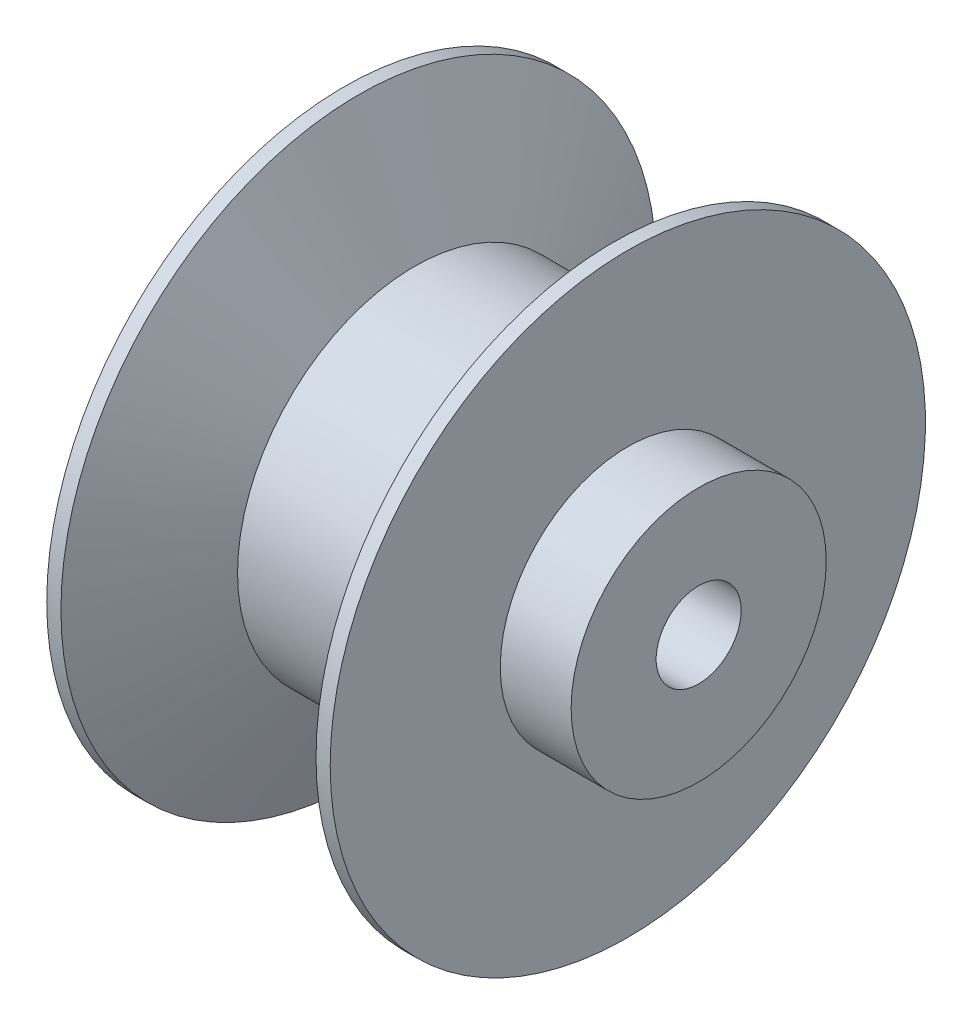
SolidWorks part; units mm, degrees
ref_plane "Plan de face" through (0, 0, 0) normal (0, 0, 1) x (1, 0, 0)
ref_plane "Plan de dessus" through (0, 0, 0) normal (0, 1, 0) x (1, 0, 0)
ref_plane "Plan de droite" through (0, 0, 0) normal (1, 0, 0) x (0, 0, -1)
sketch "Esquisse1" plane through (0, 0, 0) normal (0, 0, 1) x (1, 0, 0)
  line L0 (-128.7234, 0) -> (81.5011, 0) construction
  line L1 (-55.6577, 42) -> (-53.6577, 42)
  line L2 (-53.6577, 42) -> (-45.7304, 25)
  line L3 (-45.7304, 25) -> (-25.5849, 25)
  line L4 (-55.6577, 42) -> (-55.6577, 18)
  line L5 (-65.6577, 3) -> (-5.6577, 3)
  line L6 (-55.6577, 18) -> (-65.6577, 18)
  line L7 (-65.6577, 18) -> (-65.6577, 3)
  line L9 (-5.6577, 18) -> (-5.6577, 3)
  line L10 (-15.6577, 18) -> (-5.6577, 18)
  line L11 (-15.6577, 42) -> (-15.6577, 18)
  line L12 (-17.6577, 42) -> (-25.5849, 25)
  line L13 (-15.6577, 42) -> (-17.6577, 42)
  point P7 (-35.6577, 25)
  point P16 (-35.6577, 3)
  point P18 (-35.6577, 25)
  point P19 (-35.6577, 3)
  point P21 (-35.6577, 25)
  dimension "D1" = 0
  dimension "D2" = 25
  dimension "D3" = 42
  dimension "D4" = 0
  dimension "D5" = 2
  dimension "D6" = 3
  dimension "D7" = 10
  dimension "D8" = 15
  dimension "D9" = 20
  dimension "D10" = 115
revolve "Révolution1" add sketch "Esquisse1" angle 360 about L0
sketch "Esquisse2" plane through (-5.6577, 0, 0) normal (1, 0, 0) x (0, 0, -1)
  circle A0 centre (0, 0) radius 6
  dimension "D1" = 12
extrude "Enlèv. mat.-Extru.1" cut sketch "Esquisse2" against normal blind 40
